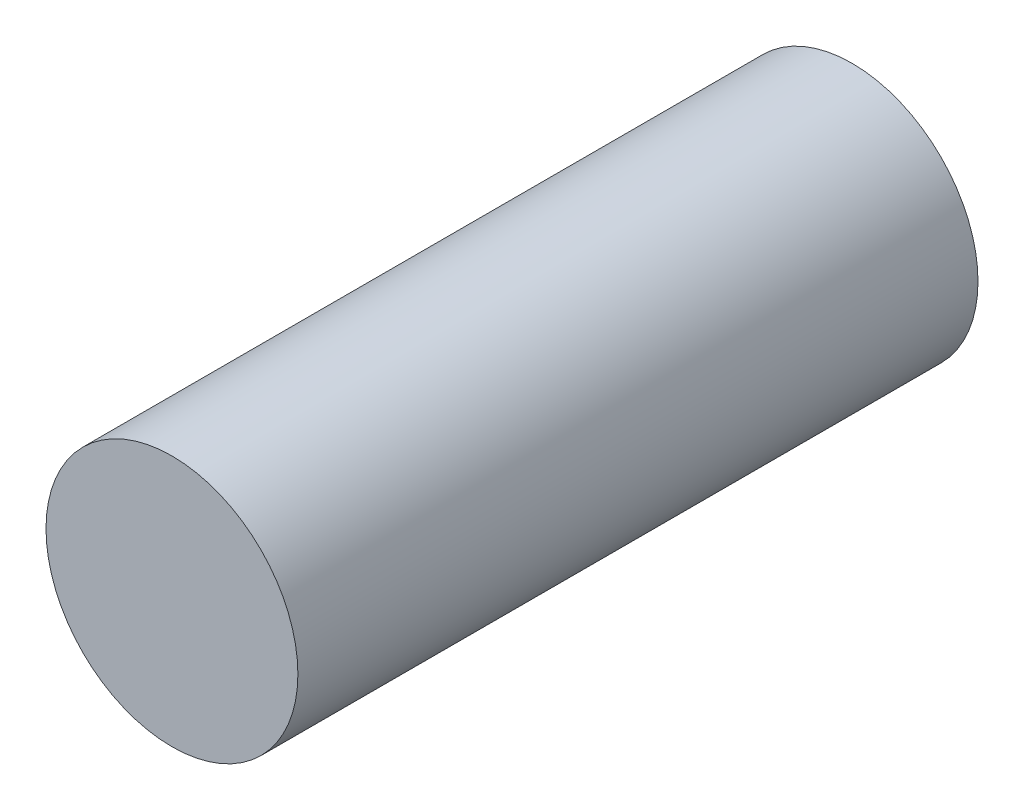
SolidWorks part; units mm, degrees
ref_plane "Front Plane" through (0, 0, 0) normal (0, 0, 1) x (1, 0, 0)
ref_plane "Top Plane" through (0, 0, 0) normal (0, 1, 0) x (1, 0, 0)
ref_plane "Right Plane" through (0, 0, 0) normal (1, 0, 0) x (0, 0, -1)
sketch "Sketch2" plane through (0, 0, 0) normal (0, 0, 1) x (1, 0, 0)
  circle A0 centre (0, 0) radius 6.35
  dimension "D1" = 12.7
extrude "Boss-Extrude1" add sketch "Sketch2" along normal blind 34.29
